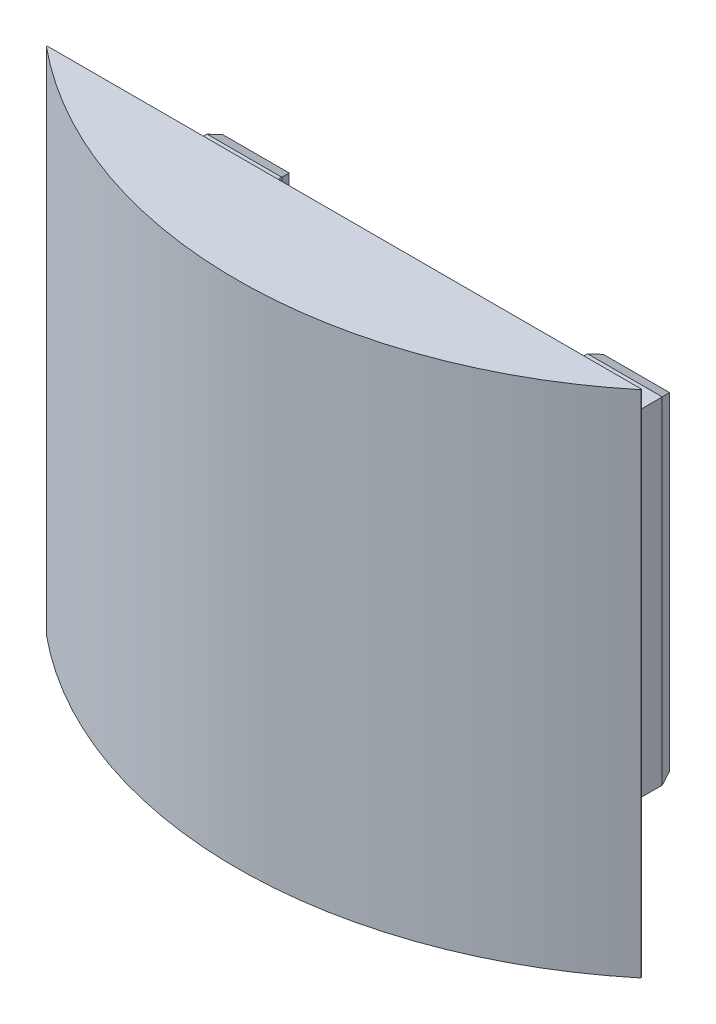
SolidWorks part; units mm, degrees
ref_plane "Спереди" through (0, 0, 0) normal (0, 0, 1) x (1, 0, 0)
ref_plane "Сверху" through (0, 0, 0) normal (0, 1, 0) x (1, 0, 0)
ref_plane "Справа" through (0, 0, 0) normal (1, 0, 0) x (0, 0, -1)
sketch "Sketch2" plane through (0, 0, 0) normal (0, 0, 1) x (1, 0, 0)
  line L1 (26.8, -19.8) -> (-26.8, -19.8)
  line L2 (26.8, -19.8) -> (26.8, 19.8)
  line L3 (26.8, 19.8) -> (-26.8, 19.8)
  line L4 (-26.8, -19.8) -> (-26.8, 19.8)
  line L5 (26.8, -19.8) -> (-26.8, 19.8) construction
  line L6 (26.8, 19.8) -> (-26.8, -19.8) construction
  point P0 (0, 0)
  dimension "D1" = 53.6
  dimension "D2" = 39.6
extrude "Boss-Extrude1" add sketch "Sketch2" along normal blind 12
sketch "Sketch3" plane through (0, 0, 12) normal (0, 0, 1) x (1, 0, 0)
  line L0 (0, 19.8) -> (0, -19.8) construction
  line L1 (35, -30) -> (-35, -30)
  line L2 (35, -30) -> (35, 30)
  line L3 (35, 30) -> (-35, 30)
  line L4 (-35, -30) -> (-35, 30)
  line L5 (35, -30) -> (-35, 30) construction
  line L6 (35, 30) -> (-35, -30) construction
  line L7 (26.8, 19.8) -> (-26.8, 19.8) construction
  line L8 (-26.8, -19.8) -> (26.8, -19.8) construction
  point P0 (0, 0)
  point P7 (0, 0)
  dimension "D1" = 70
  dimension "D2" = 60
  dimension "D3" = 0
extrude "Boss-Extrude2" add sketch "Sketch3" along normal blind 0.1
sketch "Sketch4" plane through (0, 19.8, 0) normal (0, 1, 0) x (1, 0, 0)
  line L0 (26.8, -4.6) -> (-26.8, -4.6) construction
  line L1 (26.8, -12) -> (26.8, 0) construction
  line L2 (-26.8, -12) -> (-26.8, 0) construction
  line L3 (26.8, -12) -> (-26.8, -12) construction
  circle A0 centre (22.5, -4.6) radius 2.1
  circle A1 centre (-22.5, -4.6) radius 2.1
  point P12 (0, -4.6)
  dimension "D2" = 4.2
  dimension "D3" = 4.2
  dimension "D1" = 7.4
  dimension "D4" = 45
  dimension "D5" = 22.5
extrude "Cut-Extrude1" cut sketch "Sketch4" against normal through all
sketch "Sketch5" plane through (0, 0, 0) normal (0, 0, -1) x (-1, 0, 0)
  line L0 (-26.8, 19.8) -> (26.8, 19.8) construction
  line L1 (18, -19.8) -> (-18, -19.8)
  line L2 (18, -19.8) -> (18, 19.8)
  line L3 (18, 19.8) -> (-18, 19.8)
  line L4 (-18, -19.8) -> (-18, 19.8)
  line L5 (18, -19.8) -> (-18, 19.8) construction
  line L6 (18, 19.8) -> (-18, -19.8) construction
  point P0 (0, 0)
  dimension "D1" = 36
extrude "Cut-Extrude2" cut sketch "Sketch5" against normal up to surface (12 mm away) up to face at (0, 0, 12)
chamfer "Chamfer1" distance 0.5 angle 70 8 edges at (26.8, 0, 0) (22.4, 19.8, 0) (18, 0, 0) (22.4, -19.8, 0) (-26.8, 0, 0) (-22.4, -19.8, 0) (-18, 0, 0) (-22.4, 19.8, 0)
sketch "Sketch6" plane through (0, 30, 0) normal (0, 1, 0) x (1, 0, 0)
  line L0 (35, -12.1) -> (-35, -12.1)
  arc A0 (35, -12.1) -> (-35, -12.1) centre (0, 30.3264) cw
  dimension "D1" = 55
extrude "Boss-Extrude3" add sketch "Sketch6" against normal up to surface (60 mm away) up to face at (0, -30, 12.05)
